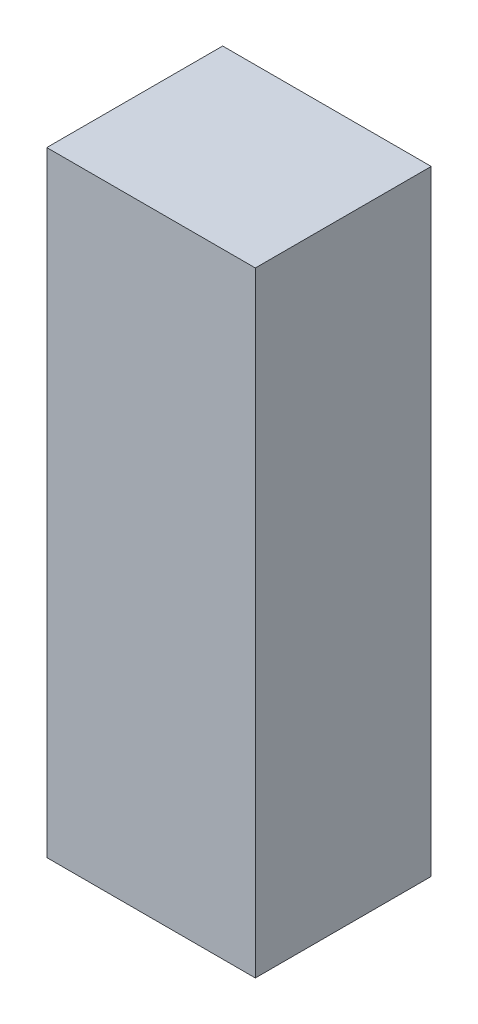
SolidWorks part; units mm, degrees
ref_plane "Front" through (0, 0, 0) normal (0, 0, 1) x (1, 0, 0)
ref_plane "Top" through (0, 0, 0) normal (0, 1, 0) x (1, 0, 0)
ref_plane "Right" through (0, 0, 0) normal (1, 0, 0) x (0, 0, -1)
sketch "Sketch1" plane through (0, 0, 0) normal (0, 1, 0) x (1, 0, 0)
  line L1 (0, 0) -> (46.6, 0)
  line L2 (0, 0) -> (0, 39.3)
  line L3 (0, 39.3) -> (46.6, 39.3)
  line L4 (46.6, 0) -> (46.6, 39.3)
  dimension "D1" = 39.3
  dimension "D2" = 46.6
extrude "Boss-Extrude1" add sketch "Sketch1" along normal blind 137.4
